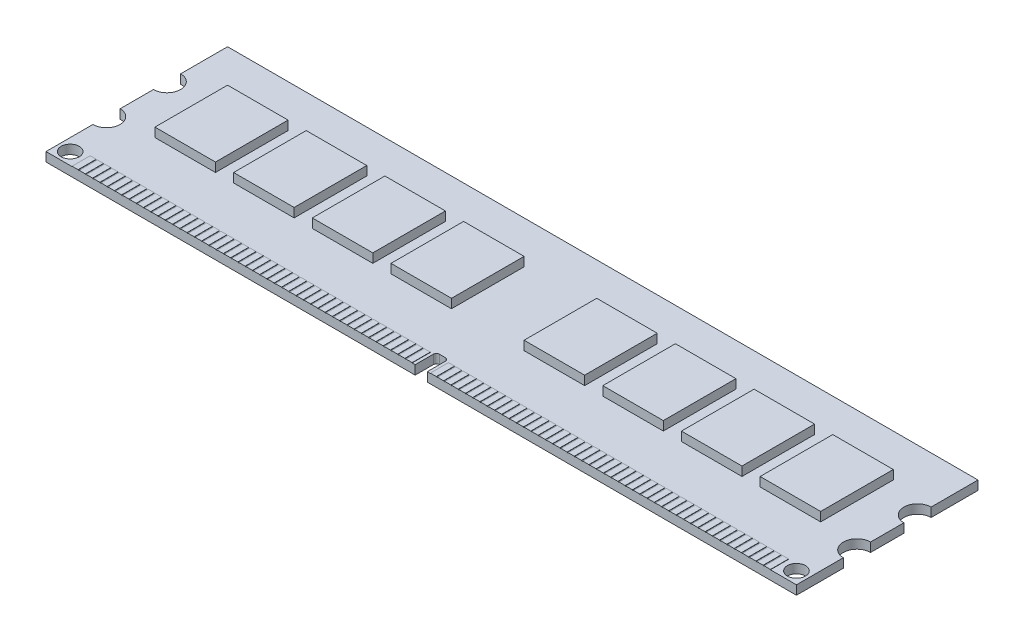
SolidWorks part; units mm, degrees
ref_plane "Front Plane" through (0, 0, 0) normal (0, 0, 1) x (1, 0, 0)
ref_plane "Top Plane" through (0, 0, 0) normal (0, 1, 0) x (1, 0, 0)
ref_plane "Right Plane" through (0, 0, 0) normal (1, 0, 0) x (0, 0, -1)
sketch "Sketch1" plane through (0, 0, 0) normal (0, 1, 0) x (1, 0, 0)
  line L0 (1, 0) -> (1, 3)
  line L1 (1, 0) -> (62, 0)
  line L2 (0, 3.5) -> (0, 30)
  line L3 (0, 30) -> (62, 30)
  line L4 (62, 0) -> (62, 7.75)
  line L5 (0.5, 3.5) -> (0, 3.5)
  line L6 (62, 12.25) -> (62, 17.75)
  line L7 (62, 22.25) -> (62, 30)
  arc A0 (62, 22.25) -> (62, 17.75) centre (62, 20) ccw
  arc A1 (62, 12.25) -> (62, 7.75) centre (62, 10) ccw
  circle A2 centre (60, 2) radius 1.5
  arc A3 (0.5, 3.5) -> (1, 3) centre (0.5, 3) cw
  point P16 (1, 3.5)
  dimension "D3" = 10
  dimension "D4" = 10
  dimension "D5" = 4.5
  dimension "D6" = 4.5
  dimension "D7" = 3
  dimension "D8" = 2
  dimension "D9" = 2
  dimension "D12" = 0.5
  dimension "D1" = 30
  dimension "D10" = 3.5
  dimension "D11" = 1
extrude "Boss-Extrude1" add sketch "Sketch1" along normal blind 1.5
sketch "Sketch2" plane through (0, 1.5, 0) normal (0, 1, 0) x (1, 0, 0)
  line L0 (1, 0) -> (62, 0) construction
  line L1 (1.5, 0) -> (2.5, 0)
  line L2 (1.5, 0) -> (1.5, 3)
  line L3 (1.5, 3) -> (2.5, 3)
  line L4 (2.5, 0) -> (2.5, 3)
  dimension "D1" = 1
  dimension "D2" = 3
  dimension "D3" = 0.5
extrude "Boss-Extrude2" add sketch "Sketch2" along normal blind 0.05
pattern_linear "LPattern1" count 47 spacing 1.2 along (1, 0, 0) of "Boss-Extrude2"
sketch "Sketch3" plane through (0, 1.5, 0) normal (0, 1, 0) x (1, 0, 0)
  line L0 (62, 30) -> (0, 30) construction
  line L1 (45, 23) -> (55, 23)
  line L2 (45, 23) -> (45, 11)
  line L3 (45, 11) -> (55, 11)
  line L4 (55, 23) -> (55, 11)
  line L5 (62, 22.25) -> (62, 30) construction
  point P8 (62, 26.125)
  dimension "D1" = 10
  dimension "D2" = 12
  dimension "D3" = 7
  dimension "D4" = 7
extrude "Boss-Extrude3" add sketch "Sketch3" along normal blind 1.5
pattern_linear "LPattern2" count 4 spacing 13 along (-1, 0, 0) of "Boss-Extrude3"
mirror "Mirror1" about plane through (0, 0, 0) normal (1, 0, 0) of "Boss-Extrude3", "LPattern1", "Boss-Extrude2", "Boss-Extrude1", "LPattern2"
